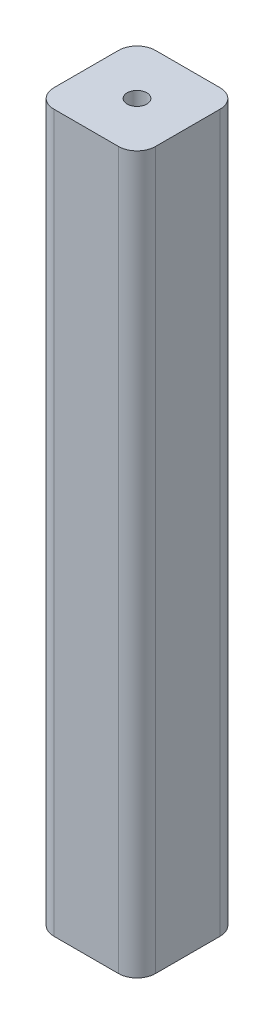
SolidWorks part; units mm, degrees
ref_plane "前视基准面" through (0, 0, 0) normal (0, 0, 1) x (1, 0, 0)
ref_plane "上视基准面" through (0, 0, 0) normal (0, 1, 0) x (1, 0, 0)
ref_plane "右视基准面" through (0, 0, 0) normal (1, 0, 0) x (0, 0, -1)
other "Configuration Table"
sketch "草图2" plane through (0, 0, 0) normal (0, 1, 0) x (1, 0, 0)
  line L1 (-22.0014, 18.6956) -> (21.9986, 18.6956)
  line L2 (-22.0014, 18.6956) -> (-22.0014, -25.3044)
  line L3 (-22.0014, -25.3044) -> (21.9986, -25.3044)
  line L4 (21.9986, 18.6956) -> (21.9986, -25.3044)
  dimension "D1" = 44
extrude "凸台-拉伸1" add sketch "草图2" along normal blind 310
sketch "草图3" plane through (0, 310, 0) normal (0, 1, 0) x (1, 0, 0)
  line L0 (-22.0014, 18.6956) -> (-22.0014, -25.3044) construction
  line L1 (21.9986, 18.6956) -> (-22.0014, 18.6956) construction
  point P0 (-0.0014, -3.3044)
  dimension "D1" = 22
  dimension "D2" = 22
hole_wizard "M10 螺纹孔1" positions "草图3" profile "草图4" tap size "M10" standard "GB"
sketch "草图4" plane through (-0.0014, 310, 3.3044) normal (1, 0, 0) x (0, 0, 1)
  line L0 (0, 0) -> (0, 27.5537)
  line L1 (0, 27.5537) -> (4.25, 25)
  line L2 (4.25, 25) -> (4.25, 0)
  line L5 (4.25, 0) -> (0, 0)
  line L10 (0, 27.5537) -> (-4.25, 25) construction
  line L11 (0, -6.35) -> (0, 107.95) construction
  dimension "螺纹孔钻头直径" = 8.5
  dimension "螺纹孔钻头深度" = 25
  dimension "导头角度" = 118
cosmetic thread "孔螺蚊线1" parameters "D1"=40, "D2"=10
sketch "草图5" plane through (0, 0, 0) normal (0, -1, 0) x (1, 0, 0)
  line L0 (-13.0014, 25.3044) -> (-13.0014, -18.6956) construction
  line L1 (-22.0014, 25.3044) -> (21.9986, 25.3044) construction
  line L2 (21.9986, -18.6956) -> (-22.0014, -18.6956) construction
  line L3 (21.9986, 25.3044) -> (21.9986, -18.6956) construction
  line L4 (12.9986, 25.3044) -> (12.9986, -18.6956) construction
  line L5 (-22.0014, -18.6956) -> (-22.0014, 25.3044) construction
  line L6 (-22.0014, 16.3044) -> (21.9986, 16.3044) construction
  line L7 (-22.0014, -9.6956) -> (21.9986, -9.6956) construction
  point P16 (-13.0014, 16.3044)
  point P17 (12.9986, 16.3044)
  point P18 (-13.0014, -9.6956)
  point P19 (12.9986, -9.6956)
  dimension "D1" = 9
  dimension "D2" = 9
  dimension "D3" = 9
  dimension "D4" = 9
hole_wizard "M6 螺纹孔1" positions "3D草图3" profile "草图7" tap size "M6" standard "GB"
sketch3d "3D草图3"
  point P0 (-13.0014, 0, 16.3044)
  point P3 (12.9986, 0, 16.3044)
  point P6 (12.9986, 0, -9.6956)
  point P9 (-13.0014, 0, -9.6956)
sketch "草图7" plane through (-13.0014, 0, 16.3044) normal (1, 0, 0) x (0, 0, -1)
  line L0 (0, 0) -> (0, 41.5022)
  line L1 (0, 41.5022) -> (2.5, 40)
  line L2 (2.5, 40) -> (2.5, 0)
  line L5 (2.5, 0) -> (0, 0)
  line L10 (0, 41.5022) -> (-2.5, 40) construction
  line L11 (0, -6.35) -> (0, 107.95) construction
  dimension "螺纹孔钻头直径" = 5
  dimension "螺纹孔钻头深度" = 40
  dimension "导头角度" = 118
cosmetic thread "孔螺蚊线2" parameters "D1"=39, "D2"=6
cosmetic thread "孔螺蚊线3" parameters "D1"=39, "D2"=6
cosmetic thread "孔螺蚊线4" parameters "D1"=39, "D2"=6
cosmetic thread "孔螺蚊线5" parameters "D1"=39, "D2"=6
fillet "圆角1" radius 8 4 edges at (-22.0014, 155, 25.3044) (21.9986, 155, 25.3044) (21.9986, 155, -18.6956) (-22.0014, 155, -18.6956)
